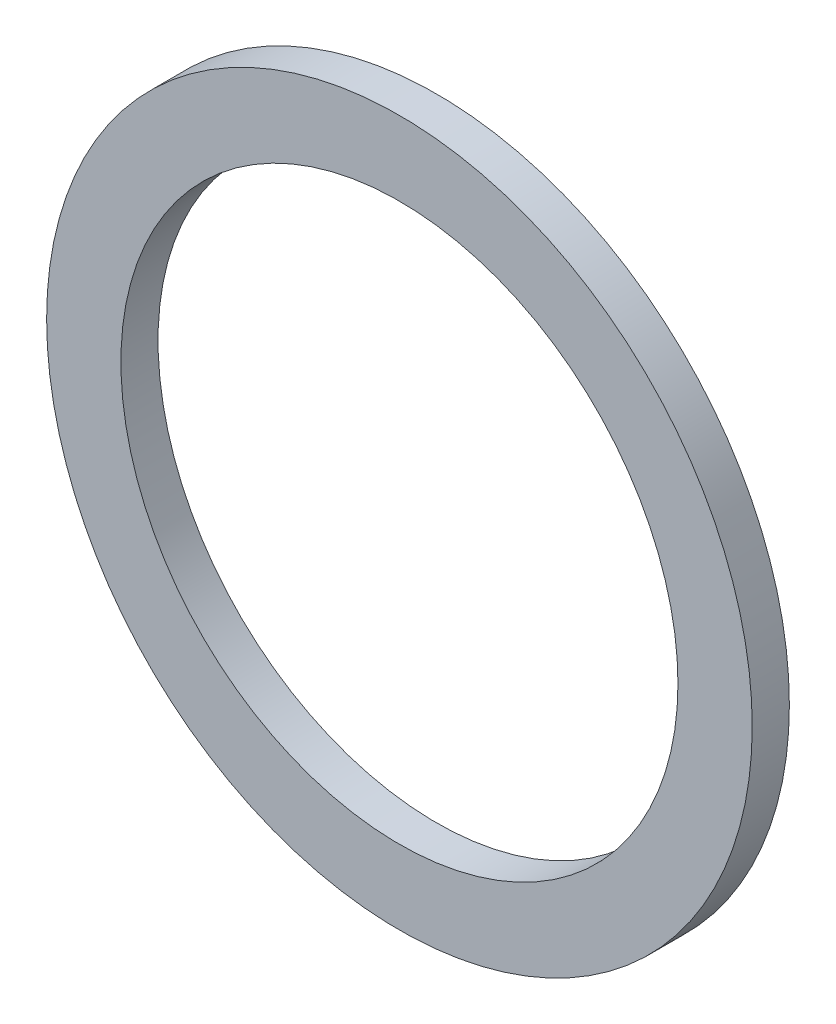
SolidWorks part; units mm, degrees
material "2024 Сплав"
ref_plane "Спереди" through (0, 0, 0) normal (0, 0, 1) x (1, 0, 0)
ref_plane "Сверху" through (0, 0, 0) normal (0, 1, 0) x (1, 0, 0)
ref_plane "Справа" through (0, 0, 0) normal (1, 0, 0) x (0, 0, -1)
sketch "Эскиз1" plane through (0, 0, 0) normal (0, 1, 0) x (1, 0, 0)
  line L0 (-7.5, 0) -> (-9.5, 0)
  line L1 (-9.5, 0) -> (-9.5, 1)
  line L2 (-9.5, 1) -> (-7.5, 1)
  line L3 (-7.5, 1) -> (-7.5, 0)
  line L4 (0, 0) -> (0, 50000) construction
  point P6 (-7.5, 0.5)
  dimension "D1" = 9.5
  dimension "D2" = 1
  dimension "D3" = 7.5
revolve "Повернуть1" add sketch "Эскиз1" angle 360 about L4
